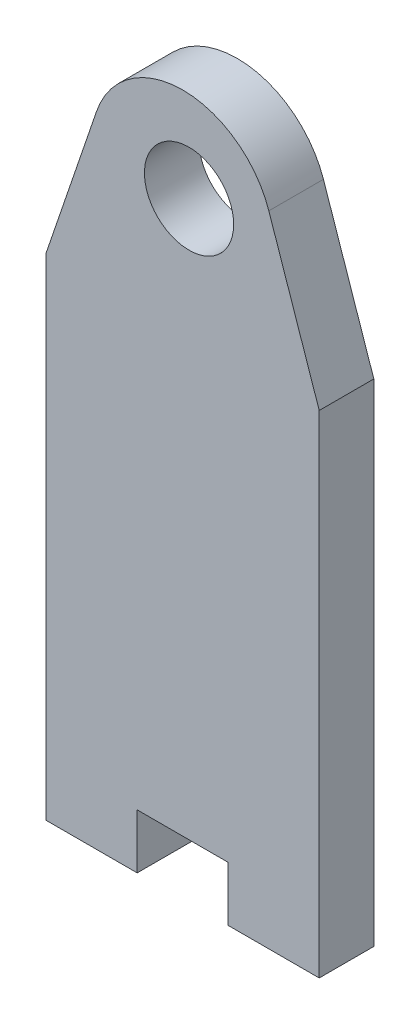
SolidWorks part; units mm, degrees
ref_plane "Alzado" through (0, 0, 0) normal (0, 0, 1) x (1, 0, 0)
ref_plane "Planta" through (0, 0, 0) normal (0, 1, 0) x (1, 0, 0)
ref_plane "Vista lateral" through (0, 0, 0) normal (1, 0, 0) x (0, 0, -1)
sketch "Model" plane through (0, 0, 0) normal (0, 0, 1) x (1, 0, 0)
  line L0 (47.7323, 49.8642) -> (50.5, 41.75)
  line L1 (50.5, 41.75) -> (50.5, 27.75)
  line L2 (50.5, 27.75) -> (50.5, 14.75)
  line L3 (50.5, 14.75) -> (45.5, 14.75)
  line L4 (45.5, 14.75) -> (45.5, 17.75)
  line L5 (45.5, 17.75) -> (40.5, 17.75)
  line L6 (40.5, 17.75) -> (40.5, 14.75)
  line L7 (40.5, 14.75) -> (35.5, 14.75)
  line L8 (35.5, 14.75) -> (35.5, 27.75)
  line L9 (35.5, 27.75) -> (35.5, 41.75)
  line L10 (35.5, 41.75) -> (38.2677, 49.8642)
  circle A0 centre (43.3486, 48.25) radius 2.45
  arc A1 (47.7323, 49.8642) -> (38.2677, 49.8642) centre (43, 48.25) ccw
extrude "Saliente-Extruir1" add sketch "Model" along normal blind 3
